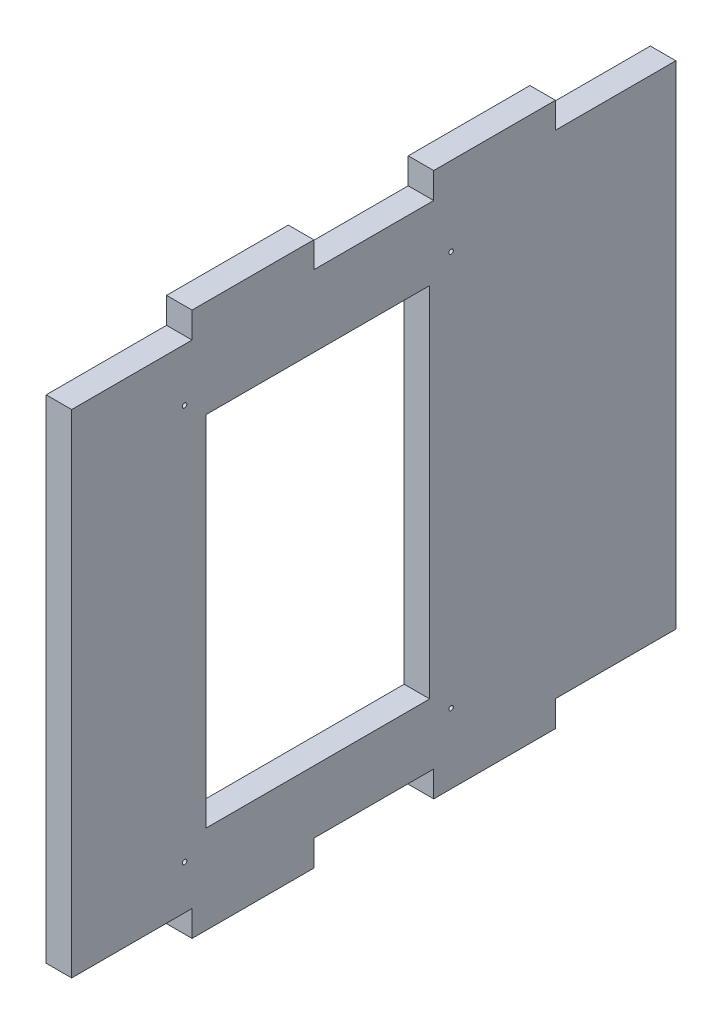
SolidWorks part; units mm, degrees
ref_plane "Front Plane" through (0, 0, 0) normal (0, 0, 1) x (1, 0, 0)
ref_plane "Top Plane" through (0, 0, 0) normal (0, 1, 0) x (1, 0, 0)
ref_plane "Right Plane" through (0, 0, 0) normal (1, 0, 0) x (0, 0, -1)
sketch "Sketch1" plane through (0, 0, 0) normal (1, 0, 0) x (0, 0, -1)
  line L1 (0, 0) -> (135, 0)
  line L2 (0, 0) -> (0, 122)
  line L3 (0, 122) -> (135, 122)
  line L4 (135, 0) -> (135, 122)
sketch "Sketch2" plane through (0, 0, 0) normal (1, 0, 0) x (0, 0, -1)
  line L0 (0, 116) -> (27, 116)
  line L1 (0, 0) -> (0, 122) construction
  line L2 (27, 116) -> (27, 121.7)
  line L4 (27, 121.7) -> (54, 121.7)
  line L5 (54, 121.7) -> (54, 116)
  line L6 (54, 116) -> (81, 116)
  line L7 (81, 116) -> (81, 121.7)
  line L8 (81, 121.7) -> (108, 121.7)
  line L9 (108, 121.7) -> (108, 116)
  line L10 (108, 116) -> (135, 116)
  line L11 (135, 0) -> (135, 122) construction
  line L12 (135, 116) -> (135, 130)
  line L13 (135, 130) -> (0, 130)
  line L14 (0, 130) -> (0, 116)
  line L16 (0, -8) -> (0, 6)
  line L17 (135, -8) -> (0, -8)
  line L18 (135, 6) -> (135, -8)
  line L19 (108, 6) -> (135, 6)
  line L20 (108, 0.3) -> (108, 6)
  line L21 (81, 0.3) -> (108, 0.3)
  line L22 (81, 6) -> (81, 0.3)
  line L23 (54, 6) -> (81, 6)
  line L24 (54, 0.3) -> (54, 6)
  line L25 (27, 0.3) -> (54, 0.3)
  line L26 (27, 6) -> (27, 0.3)
  line L27 (0, 6) -> (27, 6)
extrude "Boss-Extrude1" add sketch "Sketch1" along normal blind 5.7
sketch "Hole" plane through (0, 0, 0) normal (1, 0, 0) x (0, 0, -1)
  line L0 (80, 100) -> (30, 20) construction
  line L1 (30, 100) -> (80, 100)
  line L2 (30, 100) -> (30, 20)
  line L3 (30, 20) -> (80, 20)
  line L4 (80, 100) -> (80, 20)
  line L5 (30, 100) -> (80, 20) construction
sketch "Screw Locations" plane through (0, 0, 0) normal (1, 0, 0) x (0, 0, -1)
  line L7 (25.23, 15.83) -> (84.77, 15.83) construction
  line L8 (25.23, 15.83) -> (25.23, 104.17) construction
  line L9 (25.23, 104.17) -> (84.77, 104.17) construction
  line L10 (84.77, 15.83) -> (84.77, 104.17) construction
  line L11 (25.23, 15.83) -> (84.77, 104.17) construction
  line L12 (25.23, 104.17) -> (84.77, 15.83) construction
  circle A0 centre (25.23, 104.17) radius 0.5
  circle A1 centre (84.77, 104.17) radius 0.5
  circle A2 centre (25.23, 15.83) radius 0.5
  circle A3 centre (84.77, 15.83) radius 0.5
  point P4 (55, 60)
sketch "Plate Area" plane through (0, 0, 0) normal (1, 0, 0) x (0, 0, -1)
  line L7 (21.41, 107.94) -> (88.59, 107.94)
  line L8 (21.41, 107.94) -> (21.41, 12.06)
  line L9 (21.41, 12.06) -> (88.59, 12.06)
  line L10 (88.59, 107.94) -> (88.59, 12.06)
  line L11 (21.41, 107.94) -> (88.59, 12.06) construction
  line L12 (21.41, 12.06) -> (88.59, 107.94) construction
  point P5 (55, 60)
extrude "Cut-Extrude2" cut sketch "Hole" along normal blind 70
extrude "Cut-Extrude3" cut sketch "Screw Locations" along normal blind 52
sketch "Sketch4" plane through (0, 0, 0) normal (1, 0, 0) x (0, 0, -1)
  line L0 (0, 116) -> (26.9, 116)
  line L1 (0, -8) -> (0, 6)
  line L2 (26.9, 116) -> (26.9, 121.8)
  line L3 (-162, 61) -> (162, 61) construction
  line L4 (26.9, 121.8) -> (54.1, 121.8)
  line L5 (54.1, 121.8) -> (54.1, 116)
  line L6 (54.1, 116) -> (80.9, 116)
  line L7 (80.9, 116) -> (80.9, 121.8)
  line L8 (80.9, 121.8) -> (108.1, 121.8)
  line L9 (108.1, 121.8) -> (108.1, 116)
  line L10 (108.1, 116) -> (135, 116)
  line L11 (135, -8) -> (0, -8)
  line L12 (135, 116) -> (135, 130)
  line L13 (135, 130) -> (0, 130)
  line L14 (0, 130) -> (0, 116)
  line L15 (135, 6) -> (135, -8)
  line L16 (108.1, 6) -> (135, 6)
  line L17 (108.1, 0.2) -> (108.1, 6)
  line L18 (80.9, 0.2) -> (108.1, 0.2)
  line L19 (80.9, 6) -> (80.9, 0.2)
  line L20 (54.1, 6) -> (80.9, 6)
  line L21 (54.1, 0.2) -> (54.1, 6)
  line L22 (26.9, 0.2) -> (54.1, 0.2)
  line L23 (26.9, 6) -> (26.9, 0.2)
  line L24 (0, 6) -> (26.9, 6)
  point P7 (0, 61)
extrude "Cut-Extrude4" cut sketch "Sketch4" along normal up to surface (5.7 mm away) up to face at (5.7, 15.83, -84.27)
